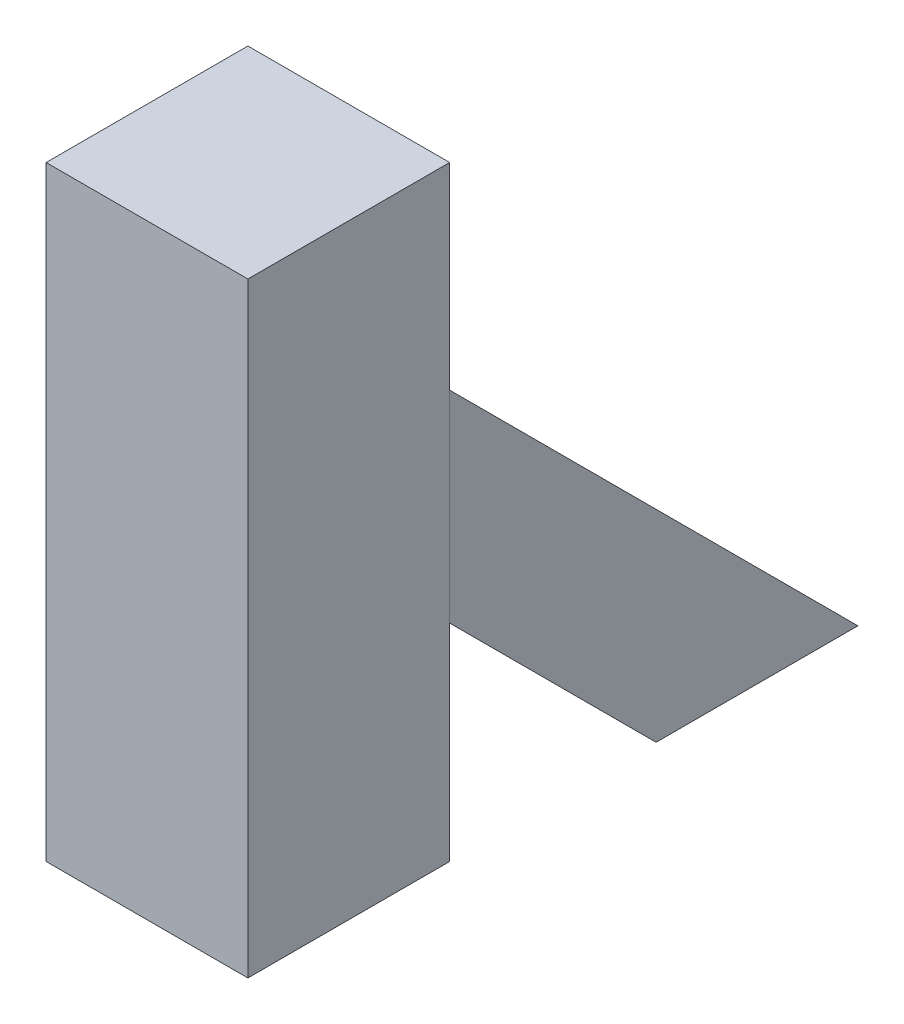
SolidWorks part; units mm, degrees
ref_plane "Front Plane" through (0, 0, 0) normal (0, 0, 1) x (1, 0, 0)
ref_plane "Top Plane" through (0, 0, 0) normal (0, 1, 0) x (1, 0, 0)
ref_plane "Right Plane" through (0, 0, 0) normal (1, 0, 0) x (0, 0, -1)
sketch "Sketch1" plane through (0, 0, 0) normal (0, 1, 0) x (1, 0, 0)
  line L1 (50, -50) -> (-50, -50)
  line L2 (50, -50) -> (50, 50)
  line L3 (50, 50) -> (-50, 50)
  line L4 (-50, -50) -> (-50, 50)
  line L5 (50, -50) -> (-50, 50) construction
  line L6 (50, 50) -> (-50, -50) construction
  point P0 (0, 0)
  dimension "D1" = 100
  dimension "D2" = 100
extrude "Boss-Extrude1" add sketch "Sketch1" along normal blind 300
sketch "Sketch2" plane through (50, 0, 0) normal (1, 0, 0) x (0, 0, -1)
  line L0 (50, 202.3132) -> (252.3132, 0)
  line L1 (50, 300) -> (50, 0) construction
  line L2 (252.3132, 0) -> (152.3132, 0)
  line L3 (152.3132, 0) -> (50, 102.3132)
  line L4 (-50, 0) -> (50, 0) construction
  line L5 (50, 202.3132) -> (50, 102.3132)
  dimension "D1" = 100
  dimension "D2" = 45
  dimension "D3" = 102.3132
extrude "Boss-Extrude2" add sketch "Sketch2" against normal blind 100 separate body
